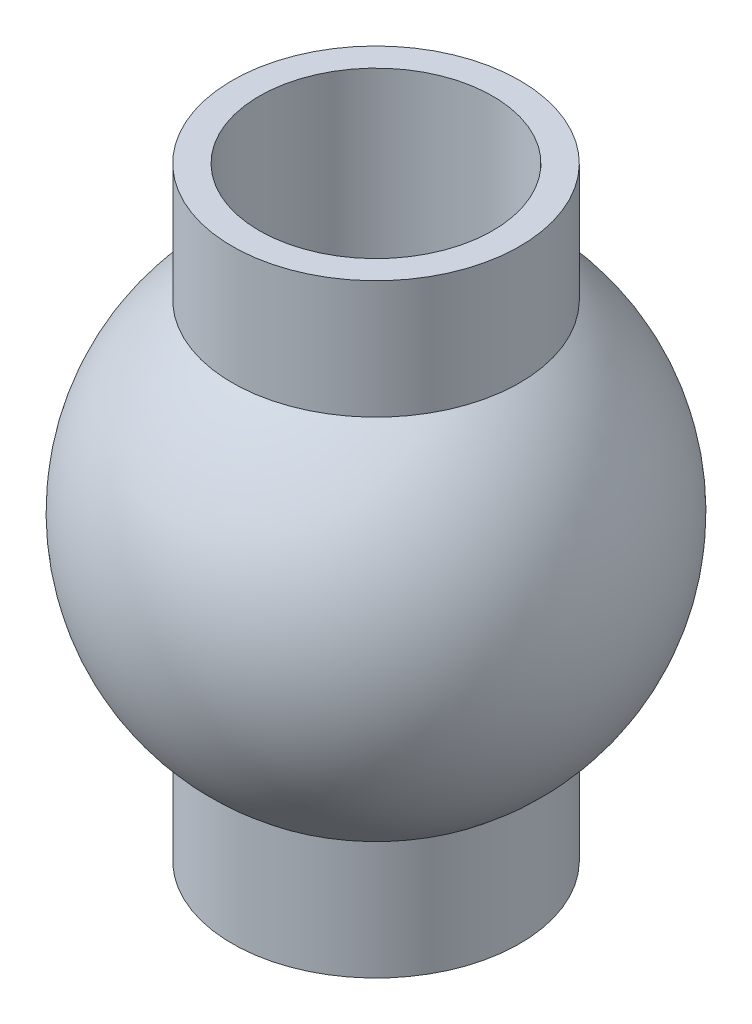
SolidWorks part; units mm, degrees
ref_plane "Front Plane" through (0, 0, 0) normal (0, 0, 1) x (1, 0, 0)
ref_plane "Top Plane" through (0, 0, 0) normal (0, 1, 0) x (1, 0, 0)
ref_plane "Right Plane" through (0, 0, 0) normal (1, 0, 0) x (0, 0, -1)
sketch "Sketch2" plane through (0, 0, 0) normal (0, 0, 1) x (1, 0, 0)
  line L0 (0, 0) -> (0, 12.9407) construction
  line L1 (0, 12.9407) -> (2.2369, 12.9407)
  line L2 (2.2369, 12.9407) -> (3.0806, 12.9407)
  line L3 (3.0806, 12.9407) -> (3.0806, 10.4086)
  line L4 (0, 6.4703) -> (6.4553, 6.4703) construction
  line L5 (3.0806, 0) -> (3.0806, 2.5321)
  line L6 (2.2369, 0) -> (3.0806, 0)
  line L7 (0, 0) -> (2.2369, 0)
  line L8 (0, 0) -> (0, 12.9407)
  arc A0 (3.0806, 2.5321) -> (3.0806, 10.4086) centre (0, 6.4703) ccw
  point P3 (0, 6.4703)
  dimension "D3" = 10
  dimension "D1" = 12.9407
  dimension "D2" = 2.2369
revolve "Revolve1" add sketch "Sketch2" angle 360 about L8
sketch "Sketch3" plane through (0, 12.9407, 0) normal (0, 1, 0) x (1, 0, 0)
  circle A0 centre (0, 0) radius 2.5
  dimension "D1" = 5
extrude "Cut-Extrude1" cut sketch "Sketch3" against normal through all
sketch3d "3DSketch2"
  line L0 (0, 0, 0) -> (0, 12.9407, 0) construction
  line L1 (0, 12.9407, 0) -> (0, 10.4086, 0) construction
  line L2 (0, 0, 0) -> (0, 12.9407, 0) construction
  point P0 (0, 12.9407, 0)
  point P1 (0, 0, 0)
  point P9 (0, 6.4703, 0)
